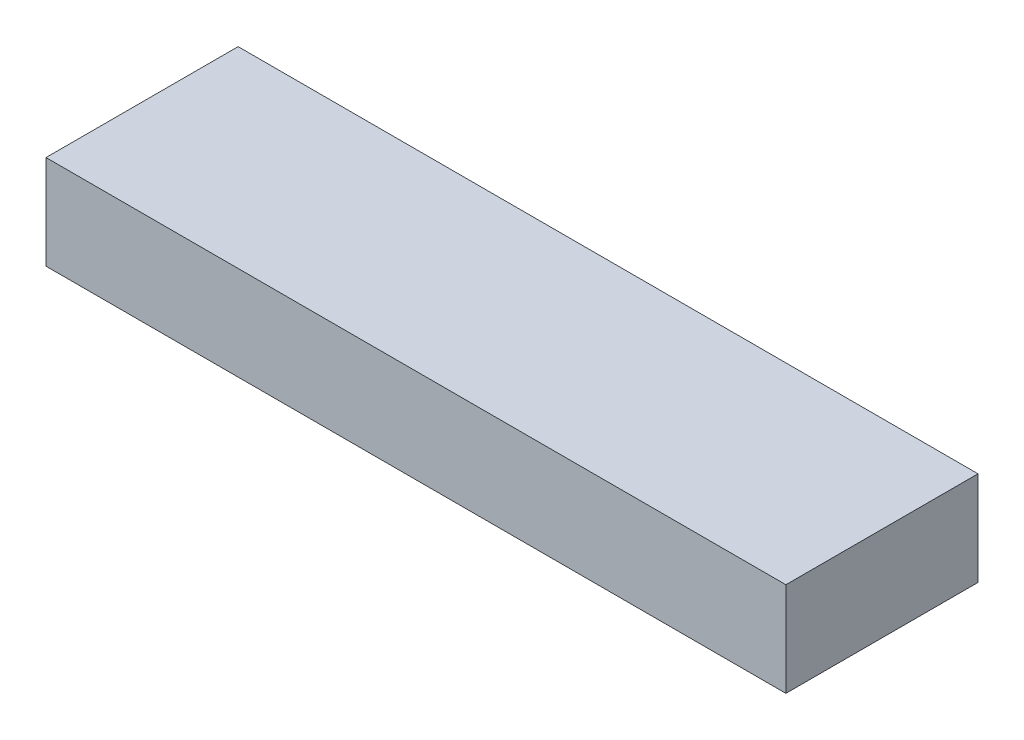
SolidWorks part; units mm, degrees
ref_plane "Front Plane" through (0, 0, 0) normal (0, 0, 1) x (1, 0, 0)
ref_plane "Top Plane" through (0, 0, 0) normal (0, 1, 0) x (1, 0, 0)
ref_plane "Right Plane" through (0, 0, 0) normal (1, 0, 0) x (0, 0, -1)
sketch "Sketch1" plane through (0, 0, 0) normal (0, 1, 0) x (1, 0, 0)
  line L1 (570, -148) -> (-570, -148)
  line L2 (570, -148) -> (570, 148)
  line L3 (570, 148) -> (-570, 148)
  line L4 (-570, -148) -> (-570, 148)
  line L5 (570, -148) -> (-570, 148) construction
  line L6 (570, 148) -> (-570, -148) construction
  point P0 (0, 0)
  dimension "D1" = 1140
  dimension "D2" = 296
extrude "Boss-Extrude1" add sketch "Sketch1" along normal blind 145
equation "\"thickness 1\" = 2"
equation "\"thickness 2\"= 3"
equation "\"connecting flange\"= 35"
equation "\"main length\"= 1200"
equation "\"main width\"= 1200"
equation "\"divider panel distance offset\"= 296"
equation "\"access hatch length\" = \"access hatch cutout length\" + \"access hatch offset\" * 2"
equation "\"access hatch width\" = \"access hatch cutout width\" + \"access hatch offset\" * 2"
equation "\"side panel length\"= 1200"
equation "\"side panel width\"= 950"
equation "\"drift eliminator size offset\"= 5"
equation "\"drift eliminator depth\" = \"divider panel distance offset\""
equation "\"D2@Sketch1\"=\"drift eliminator depth\""
equation "\"thickness radius 1\"= 3.7366"
equation "\"connecting flange holes\"= 8"
equation "\"connecting flange hole gap\"= 100"
equation "\"cut out flange\"= 15"
equation "\"top panel slot length\"= 250"
equation "\"top panel slot width\"= 700"
equation "\"access hatch cutout length\"= 400"
equation "\"access hatch cutout width\"= 600"
equation "\"access hatch cutout offset X\"= 100"
equation "\"access hatch cutout offset Y\"= 100"
equation "\"slotted panel length\" = \"main length\" + 100"
equation "\"slotted panel width\" = \"main width\""
equation "\"slot count x\"= 4"
equation "\"slot count y\"= 9"
equation "\"slot offset\" = \"water tray depth\""
equation "\"slot length\"= 30"
equation "\"slot width\"= 200"
equation "\"slot offset x\" = \"slot length\" + \"slot offset\""
equation "\"slot offset y\" = \"slot width\" + \"slot offset\""
equation "\"guide rail flange\"= 40"
equation "\"guid rail flange mount side\"= 20"
equation "\"guid rail back length\" = \"main width\" - \"guide rail flange\" * 2"
equation "\"splash plate length\"= 400"
equation "\"splash plate width\" = \"main width\""
equation "\"splash plate air gap\"= 200"
equation "\"splash plate slot count\"= 11"
equation "\"splash plate slot length\"= 50"
equation "\"splash plate slot height\"= 50"
equation "\"splash plate slot offset\"= 65"
equation "\"water tray depth\"= 150"
equation "\"water tray width\"= 200"
equation "\"water tray panel length\"= 473"
equation "\"dimpled panel length\" = \"main length\" - 200 - \"water tray depth\"/2"
equation "\"dimpled panel top offset\" = \"water tray depth\"/2"
equation "\"dimpled panel width\" = \"main width\""
equation "\"dimple panel slot count\"= 36"
equation "\"dimple panel slot length\"= 8"
equation "\"dimple panel slot width\"= 8"
equation "\"dimple panel slot offset\"= 25"
equation "\"sump base flat section width\"= 300"
equation "\"sump upper depth\"= 300"
equation "\"sump depth\"= 550"
equation "\"leg length\" = \"sump depth\" + 150"
equation "\"leg width\"= 80"
equation "\"leg depth\"= 40"
equation "\"leg support plate size\" = \"leg width\" - \"thickness 2\" * 2"
equation "\"leg base plate thickness\"= 8"
